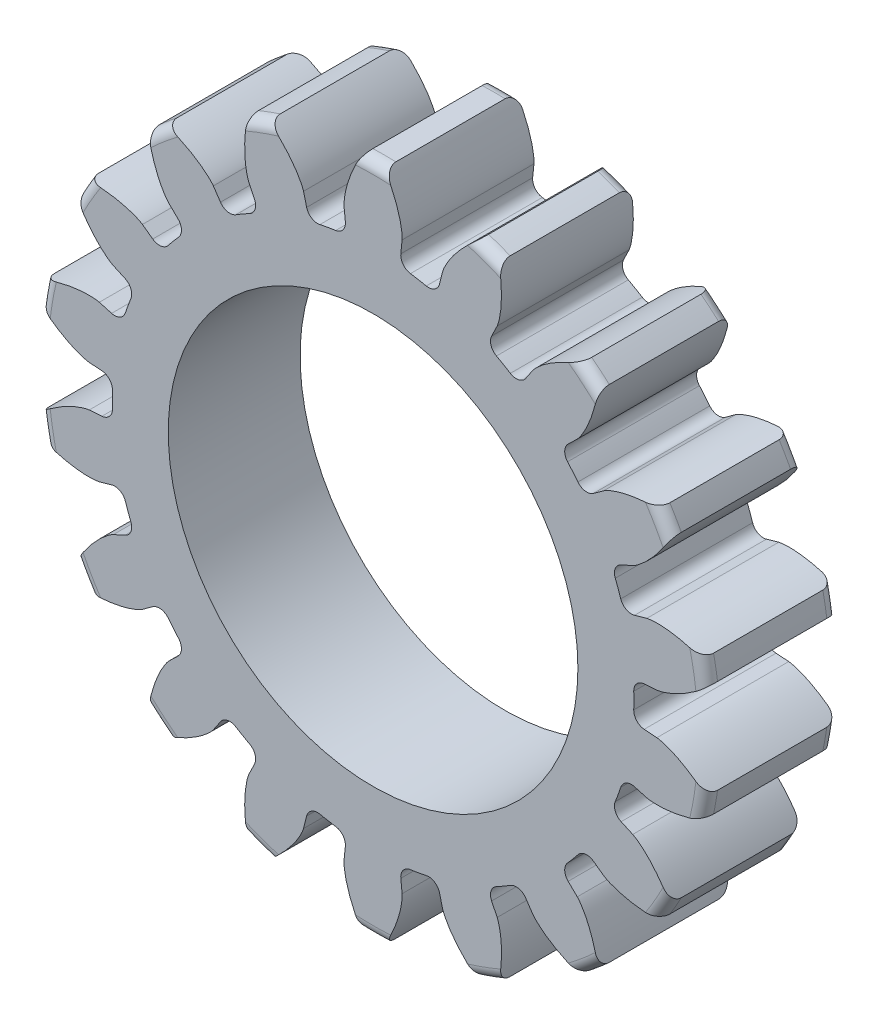
SolidWorks part; units mm, degrees
ref_plane "Front Plane" through (0, 0, 0) normal (0, 0, 1) x (1, 0, 0)
ref_plane "Top Plane" through (0, 0, 0) normal (0, 1, 0) x (1, 0, 0)
ref_plane "Right Plane" through (0, 0, 0) normal (1, 0, 0) x (0, 0, -1)
sketch "Sketch1" plane through (0, 0, 0) normal (0, 0, 1) x (1, 0, 0)
  line L0 (0, 0) -> (0, 9.525) construction
  line L1 (-3.0613, 10.6392) -> (3.0613, 8.4108) construction
  circle A0 centre (0, 0) radius 8.2021 construction
  circle A1 centre (0, 0) radius 10.5833 construction
  circle A2 centre (0, 0) radius 9.525 construction
  circle A3 centre (0, 0) radius 8.9506 construction
  circle A4 centre (0, 0) radius 2.3813 construction
  circle A5 centre (0, 0) radius 6.858 construction
  point P8 (304.8, 0)
  point P13 (228.6, 0)
  dimension "OD | Outside Diameter" = 21.1667
  dimension "Root Diameter" = 16.4042
  dimension "Gear Pitch Diameter" = 19.05
  dimension "Base Diameter" = 17.9011
  dimension "For Shaft Diameter" = 4.7625
  dimension "Hub Diameter" = 13.716
  dimension "Pressure Angle" = 20
  dimension "Number of Teeth" = 457.2
  dimension "Gear Pitch | Diametral Pitch" = 609.6
sketch "Sketch2" plane through (0, 0, 0) normal (1, 0, 0) x (0, 0, -1)
  line L0 (-6.35, 0) -> (6.35, 0) construction
  line L1 (-6.35, 10.5833) -> (6.35, 10.5833) construction
  point P2 (0, 10.5833)
  point P4 (0, 0)
  point P6 (0, 10.5833)
  dimension "Overall Width" = 12.7
  dimension "Hub Width" = 6.35
  dimension "Face Width" = 6.35
sketch "Sketch3" plane through (0, 0, 0) normal (0, 0, 1) x (1, 0, 0)
  circle A0 centre (0, 0) radius 10.5833
  circle A1 centre (0, 0) radius 10.5833 construction
extrude "Boss-Extrude1" add sketch "Sketch3" against normal blind 4.1469 and the other way up to vertex (6.35 mm away) other way up to point (0, 0, 6.35)
sketch "Sketch5" plane through (0, 0, 0) normal (1, 0, 0) x (0, 0, -1)
  line L1 (-6.35, 10.5833) -> (0, 10.5833)
  line L2 (-6.35, 10.5833) -> (-6.35, 6.858)
  line L3 (-6.35, 6.858) -> (0, 6.858)
  line L4 (0, 10.5833) -> (0, 6.858)
  line L11 (6.35, 2.3813) -> (-6.35, 2.3812)
  line L12 (6.35, 2.3813) -> (6.35, 0)
  line L13 (6.35, 0) -> (-6.35, 0)
  line L14 (-6.35, 2.3812) -> (-6.35, 0)
  point P5 (0, 2.3813)
  point P12 (0, 6.858)
revolve "Cut-Revolve1" cut sketch "Sketch5" angle 360 about L0
fillet "Fillet2" radius 0.3551 6 edges at (10.5833, 0, -4.1469) (2.3813, 0, -4.1469) (2.3812, 0, 6.35) (6.858, 0, 0) (10.5833, 0, 0) (6.858, 0, 6.35)
sketch "Sketch4" plane through (0, 0, 0) normal (0, 0, 1) x (1, 0, 0)
  line L0 (0, 0) -> (8.1806, 0.593) construction
  line L2 (0, 0) -> (8.1806, -0.593) construction
  line L4 (8.1806, 0.593) -> (8.9271, 0.6471)
  line L5 (8.9271, -0.6471) -> (8.1806, -0.593)
  arc A0 (8.1806, 0.593) -> (8.1806, -0.593) centre (0, 0) cw
  arc A3 (10.4791, 1.4815) -> (10.4791, -1.4815) centre (0, 0) cw
  circle A4 centre (0, 0) radius 10.5833 construction
  spline S0 degree 4 poles (8.9271, 0.6471) (8.9298, 0.6473) (8.9371, 0.6481) (8.951, 0.6499) (8.9735, 0.6535) (9.0022, 0.659) (9.039, 0.6671) (9.0823, 0.6779) (9.1296, 0.6912) (9.1807, 0.7071) (9.2315, 0.7243) (9.2819, 0.7426) (9.3319, 0.762) (9.3922, 0.7867) (9.464, 0.8182) (9.5473, 0.8575) (9.6409, 0.905) (9.7354, 0.9567) (9.8276, 1.0102) (9.9198, 1.0673) (10.0083, 1.1246) (10.0992, 1.1871) (10.1825, 1.2464) (10.2747, 1.3161) (10.3487, 1.3734) (10.4449, 1.4524) (10.5013, 1.5001) (10.5668, 1.5571) (10.5956, 1.5831) (10.6134, 1.599) knots 0 0 0 0 0 0.005377 0.015084 0.028532 0.04661 0.064855 0.092111 0.119476 0.146842 0.174209 0.201575 0.228941 0.256307 0.307035 0.361767 0.4165 0.471232 0.525964 0.580697 0.635429 0.690161 0.744894 0.799626 0.854358 0.909091 0.954545 1 1 1 1 1 construction
  spline S1 degree 4 poles (8.9271, 0.6471) (8.9298, 0.6473) (8.9371, 0.6481) (8.951, 0.6499) (8.9735, 0.6535) (9.0022, 0.659) (9.039, 0.6671) (9.0823, 0.6779) (9.1296, 0.6912) (9.1807, 0.7071) (9.2315, 0.7243) (9.2819, 0.7426) (9.3319, 0.762) (9.3922, 0.7867) (9.464, 0.8182) (9.5473, 0.8575) (9.6409, 0.905) (9.7354, 0.9567) (9.8276, 1.0102) (9.9198, 1.0673) (10.0083, 1.1246) (10.0992, 1.1871) (10.1825, 1.2464) (10.2747, 1.3161) (10.3487, 1.3734) (10.424, 1.4353) (10.4605, 1.4658) (10.4791, 1.4815) knots 0 0 0 0 0 0.005377 0.015084 0.028532 0.04661 0.064855 0.092111 0.119476 0.146842 0.174209 0.201575 0.228941 0.256307 0.307035 0.361767 0.4165 0.471232 0.525964 0.580697 0.635429 0.690161 0.744894 0.799626 0.854358 0.909091 0.909091 0.909091 0.909091 0.909091
  spline S2 degree 4 poles (8.9271, -0.6471) (8.9298, -0.6473) (8.9371, -0.6481) (8.951, -0.6499) (8.9735, -0.6535) (9.0022, -0.659) (9.039, -0.6671) (9.0823, -0.6779) (9.1296, -0.6912) (9.1807, -0.7071) (9.2315, -0.7243) (9.2819, -0.7426) (9.3319, -0.762) (9.3922, -0.7867) (9.464, -0.8182) (9.5473, -0.8575) (9.6409, -0.905) (9.7354, -0.9567) (9.8276, -1.0102) (9.9198, -1.0673) (10.0083, -1.1246) (10.0992, -1.1871) (10.1825, -1.2464) (10.2747, -1.3161) (10.3487, -1.3734) (10.4449, -1.4524) (10.5013, -1.5001) (10.5668, -1.5571) (10.5956, -1.5831) (10.6134, -1.599) knots 0 0 0 0 0 0.005377 0.015084 0.028532 0.04661 0.064855 0.092111 0.119476 0.146842 0.174209 0.201575 0.228941 0.256307 0.307035 0.361767 0.4165 0.471232 0.525964 0.580697 0.635429 0.690161 0.744894 0.799626 0.854358 0.909091 0.954545 1 1 1 1 1 construction
  spline S3 degree 4 poles (8.9271, -0.6471) (8.9298, -0.6473) (8.9371, -0.6481) (8.951, -0.6499) (8.9735, -0.6535) (9.0022, -0.659) (9.039, -0.6671) (9.0823, -0.6779) (9.1296, -0.6912) (9.1807, -0.7071) (9.2315, -0.7243) (9.2819, -0.7426) (9.3319, -0.762) (9.3922, -0.7867) (9.464, -0.8182) (9.5473, -0.8575) (9.6409, -0.905) (9.7354, -0.9567) (9.8276, -1.0102) (9.9198, -1.0673) (10.0083, -1.1246) (10.0992, -1.1871) (10.1825, -1.2464) (10.2747, -1.3161) (10.3487, -1.3734) (10.424, -1.4353) (10.4605, -1.4658) (10.4791, -1.4815) knots 0 0 0 0 0 0.005377 0.015084 0.028532 0.04661 0.064855 0.092111 0.119476 0.146842 0.174209 0.201575 0.228941 0.256307 0.307035 0.361767 0.4165 0.471232 0.525964 0.580697 0.635429 0.690161 0.744894 0.799626 0.854358 0.909091 0.909091 0.909091 0.909091 0.909091
  dimension "D1" = 16.4042
extrude "Cut-Extrude1" cut sketch "Sketch4" against normal through all both and the other way through all
fillet "Fillet1" radius 0.3551 2 edges at (8.1806, -0.593, -2.0735) (8.1806, 0.593, -2.0735)
pattern_circular "CirPattern1" count 18 over 360 about axis through (0, 0, 6.35) along (0, 0, -1) of "Cut-Extrude1", "Fillet1"
sketch "Sketch6" plane through (0, 0, 6.35) normal (0, 0, 1) x (1, 0, 0)
  circle A0 centre (0, 0) radius 7.6514
extrude "Cut-Extrude2" cut sketch "Sketch6" against normal up to surface (6.35 mm away) up to face at (0, 0, 0)
sketch "Sketch7" plane through (0, 0, 0) normal (0, 0, 1) x (1, 0, 0)
  circle A0 centre (0, 0) radius 6.4426
  dimension "D1" = 12.8851
extrude "Cut-Extrude3" cut sketch "Sketch7" against normal up to surface (4.1469 mm away) up to face at (0, 0, -4.1469)
scale "Scale1" scale about centroid uniform scaling yes scale factor 1.75
equation "\"Root Diameter@Sketch1\"=\"Root Diameter\""
equation "\"OD | Outside Diameter@Sketch1\"=\"Outside Diameter\""
equation "\"D1@CirPattern1\"=\"Number of Teeth\""
equation "\"Diametral Pitch\"= 24"
equation "\"Number of Teeth\"= 18"
equation "\"Pressure Angle\"=20"
equation "\"Pitch Diameter\"= \"Number of Teeth\" / \"Diametral Pitch\""
equation "\"Base Diameter\"= \"Pitch Diameter\" * cos ( \"Pressure Angle\" )"
equation "\"Outside Diameter\"= ( \"Number of Teeth\" + 2 ) / \"Diametral Pitch\""
equation "\"Dedendum\"= 1.25 / \"Diametral Pitch\""
equation "\"Root Diameter\"= \"Pitch Diameter\" - ( 2 * \"Dedendum\" )"
equation "\"Pitch Angle\"= 360deg / \"Number of Teeth\""
equation "\"Alpha\"= sqr ( \"Pitch Diameter\" ^ 2 - \"Base Diameter\" ^ 2 ) / \"Base Diameter\" * 180 / PI - \"Pressure Angle\""
equation "\"Beta\"= ( \"Pitch Angle\" / 4 - \"Alpha\" )"
equation "\"Phi\"= sqr ( ( \"Outside Diameter\" / 2 ) ^ 2 - ( \"Base Diameter\" / 2 ) ^ 2 ) / ( \"Base Diameter\" / 2 )"
equation "\"Addendum\"= 1 / \"Diametral Pitch\""
equation "\"WorkingDepth\"= 2 / \"Diametral Pitch\""
equation "\"WholeDepth\"= 2.25 / \"Diametral Pitch\""
equation "\"Clearance\"= 0.25 / \"Diametral Pitch\""
equation "\"ToothThickness\"= ( pi * 2 ) / \"Diametral Pitch\""
equation "\"CircularPitch\"= pi / \"Diametral Pitch\""
equation "\"Number of Teeth@Sketch1\"=\"Number of Teeth\""
equation "\"Gear Pitch | Diametral Pitch@Sketch1\"=\"Diametral Pitch\""
equation "\"Pressure Angle@Sketch1\"=\"Pressure Angle\""
equation "\"Gear Pitch Diameter@Sketch1\"=\"Pitch Diameter\""
equation "\"Base Diameter@Sketch1\"=\"Base Diameter\""
equation "\"Fillet\"= \"Clearance\" * cos ( \"Pressure Angle\" ) * tan ( ( 90 + \"Pressure Angle\" ) / 2 )"
equation "\"D1@Fillet1\"=\"Fillet\""
equation "\"D1@Sketch4\"=if( \"Base Diameter\">\"Root Diameter\",\"Root Diameter\",\"Base Diameter\"-.00001)"
equation "\"D1@Fillet2\"=\"Fillet\""
